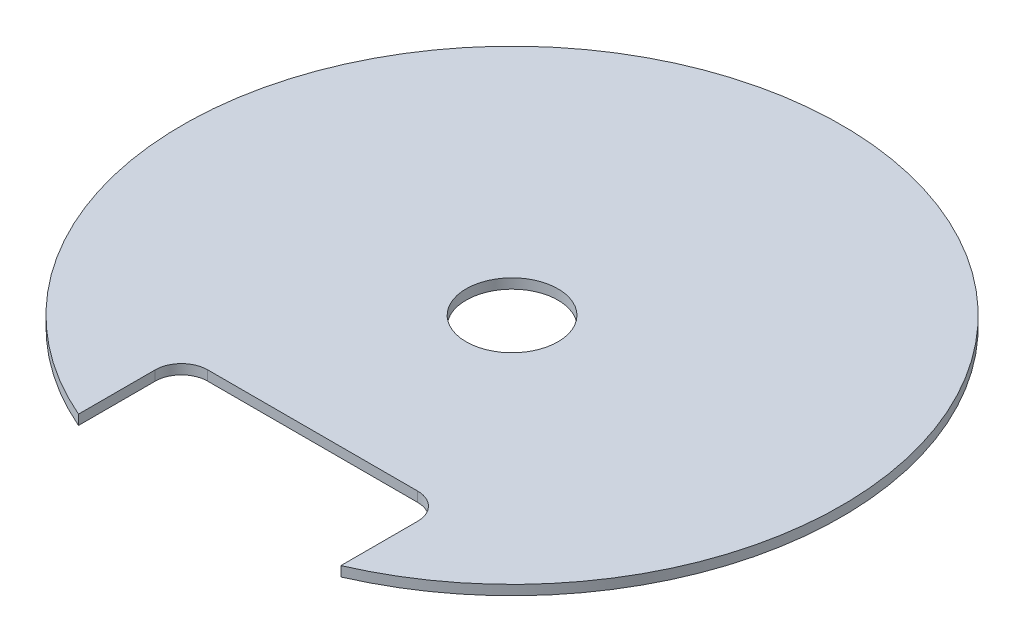
SolidWorks part; units mm, degrees
ref_plane "Front Plane" through (0, 0, 0) normal (0, 0, 1) x (1, 0, 0)
ref_plane "Top Plane" through (0, 0, 0) normal (0, 1, 0) x (1, 0, 0)
ref_plane "Right Plane" through (0, 0, 0) normal (1, 0, 0) x (0, 0, -1)
sketch "Sketch1" plane through (0, 0, 0) normal (0, 1, 0) x (1, 0, 0)
  circle A0 centre (0, 0) radius 50.25
  circle A1 centre (0, 0) radius 7
  dimension "D1" = 100.5
  dimension "D2" = 14
extrude "Boss-Extrude1" add sketch "Sketch1" against normal blind 1.5
sketch "Sketch2" plane through (0, 0, 0) normal (0, 1, 0) x (1, 0, 0)
  line L0 (-20, -46.2619) -> (-20, -34.4) construction
  line L1 (-16, -30.4) -> (16, -30.4) construction
  line L2 (20, -34.4) -> (20, -46.2619) construction
  line L3 (20, -34.4) -> (20, -46.2619)
  line L4 (-16, -30.4) -> (16, -30.4)
  line L5 (-20, -46.2619) -> (-20, -34.4)
  arc A0 (-16, -30.4) -> (-20, -34.4) centre (-16, -34.4) ccw construction
  arc A1 (20, -34.4) -> (16, -30.4) centre (16, -34.4) ccw construction
  arc A2 (20, -34.4) -> (16, -30.4) centre (16, -34.4) ccw
  arc A3 (-16, -30.4) -> (-20, -34.4) centre (-16, -34.4) ccw
  circle A4 centre (0, 0) radius 50.4 construction
  arc A5 (-20, -46.2619) -> (20, -46.2619) centre (0, 0) ccw
extrude "Cut-Extrude1" cut sketch "Sketch2" against normal through all
equation "\"pelletWidth\"= 13mm'The Width of the pellet to be dispensed"
equation "\"pelletLength\"= 26mm'The length of the pellet to be dispensed"
equation "\"pelletThickness\"= 13mm'The Thickness of the pellet to be dispensed"
equation "\"pelletRadius\"= 10mm'The roundness / radius of the pellet to be dispensed"
equation "\"rotatingPlateDiameter\"= 100mm'the diameter of the rotating plate"
equation "\"rotatingPlateHeight\"= (\"pelletThickness\"*0.9)'The thickness of the rotating plate"
equation "\"rotatingPlateDiameterAllowance\"= 0.5mm'Allowance around the edge of the rotating plate"
equation "\"rotatingPlateAgitatorDiameter\"= ( \"rotatingPlateDiameter\"-((\"pelletWidth\"*1.3)*2.5) )'The diameter of the \"agitator\" section of the rotating plate"
equation "\"rotatingPlateAgitatorHeight\"= 80mm'The height of the \"agitator\" section of the rotating plate"
equation "\"rotatingPlateAgitatorBladeThickness\"= 4mm'The thickness of the blade on the \"agitator\" section of the rotating plate"
equation "\"rotatingPlateAgitatorBladeDistance\"= ( (\"rotatingPlateAgitatorDiameter\"+ 20mm) - (\"rotatingPlateAgitatorDiameter\") )'The distance offset of the blade from the surface of the \"agitator\" section of the rotating plate"
equation "\"rotatingPlateAgitatorBladeBottomGap\"= ( \"pelletThickness\"*1.2 )'The gap between the bottom of the blade and the base of the plate on the \"agitator\" section of the rotating plate"
equation "\"rotatingPlateAgitatorBladesNumber\"= ( 3 )'The number of blades on the \"agitator\" section of the rotating plate"
equation "\"hopperBaseChamferAngle\"= 60deg'Angle of the chamfer of the Hopper base Toward the plate"
equation "\"hopperBaseLipOverhang\"= 5mm'The overhang amount of the hopper base lip"
equation "\"hopperBaseLipDepth\"= 5mm'The depth of the hopper base's overhang lip"
equation "\"hopperBaseLockNotchWidth\"= 10mm'The width of the hopper base \"lock\" notch to prevent rotation"
equation "\"hopperBaseLockNotchHeight\"= 10mm'The height of the hopper base \"lock\" notch to prevent rotation"
equation "\"hopperBaseRearNotchHeight\"= 8mm'The height of the rear snap-lock notch on the hopper base"
equation "\"hopperBaseRearNotchWidth\"= 8mm'The width of the rear snap-lock notch on the hopper base"
equation "\"hopperTankWallThickness\"= 5mm'The wall thickness of the hopper tank where pellet reserve will be stored"
equation "\"hopperTankDiameter\"= ( \"rotatingPlateDiameter\"*1.8 )'**Must be greater than \"rotatingPlateDiameter\" -- The inner diameter of the hopper tank where pellet reserve will be stored"
equation "\"hopperTankHeight\"= 200mm'The height of the hopper tank where pellet reserve will be stored"
equation "\"hopperTankCoverThickness\"= 10mm'The thickness of the Hopper Tank's cover"
equation "\"hopperTankCoverHandleLength\"= 60mm'The length of the handles on the hopper tank cover"
equation "\"hopperTankCoverHandleWidth\"= 20mm'The width of the handles on the hopper tank cover, defined as the offset from the cover's main edge"
equation "\"motorMountOffset\"= 30mm'The distance offset of the motor mount part from the hopper tank's outer edge"
equation "\"motorMountHeight\"= (\"motorHeight\" + \"motorFacePlateThickness\" + 0mm)'The height / thickness of the motor mount part"
equation "\"motorDiameter\"= 35mm'The Diameter of the main motor unit"
equation "\"motorHeight\"= 13.4mm'The height of the main motor unit"
equation "\"motorConnectorWidth\"= 10mm'The width of the motor's electrical cable connector"
equation "\"motorConnectorLength\"= 8mm'The length of the motor's electrical cable connector"
equation "\"motorConnectorHeight\"= 5mm'The height of the motor's electrical cable connector"
equation "\"motorFacePlateLength\"= 50mm'The length of the motor faceplate"
equation "\"motorFacePlateWidth\"= 10mm'The width of the motor faceplate"
equation "\"motorFacePlateThickness\"= 1mm'The thickness of the motor faceplate"
equation "\"motorFacePlateCenterRadius\"= 20mm'The rounding radius of the motor faceplate center"
equation "\"motorFacePlateEndRadius\"= 10mm'The rounding radius of the motor faceplate ends"
equation "\"motorFacePlateMountingHoleDiameter\"= 6mm'The diameter of the motor faceplate's mounting holes"
equation "\"motorFacePlateMoutingHoleDistanceBetweenHoles\"= 42mm'The distance between the center of the mounting holes"
equation "\"motorSpindleDiameter\"= 2mm'The diameter of the motor spindle"
equation "\"motorSpindleFlatFaceLength\"= 1.5mm'The length of the flat face of the motor spindle"
equation "\"motorSpindleHeight\"= 9mm'The height of the motor spindle from the face of the motor"
equation "\"motorSpindleMountDiameter\"= 12mm'The diameter of the raised mount section of the motor where the spindle is attached"
equation "\"motorSpindleMountHeight\"= 1.5mm'The height of the raised mount section of the motor where the spindle is attached"
equation "\"generalFittingTolerance\"= 0.1mm'The general fitting tolerance between contacting parts"
equation "\"D1@Sketch1\"=\"rotatingPlateDiameter\"+\"rotatingPlateDiameterAllowance\""
equation "\"D2@Sketch1\"=\"motorSpindleMountDiameter\"+2"
equation "\"D1@Boss-Extrude1\"=\"motorSpindleMountHeight\""
equation "\"rotatingPlatePelletSlotLength\"= \"pelletLength\"*1.3'The length of the slot where a pellet will be captured"
equation "\"rotatingPlatePelletSlotWidth\"= \"pelletWidth\"*1.3'The width of the slot where a pellet will be captured"
equation "\"rotatingPlateNumberOfPelletSlots\"= ( (2*pi*(\"rotatingPlateDiameter\"/2)) / ((\"rotatingPlatePelletSlotLength\"*1.1)*3) )'The maximum number of pellet slots allows in the rotating plate for proper spacing"
equation "\"rotatingPlateAgitatorTopRoundingRadius\"= 6mm'The rounding radius of the top of the \"agitator\" section of the rotating plate"
equation "\"hopperBaseInnerDiameter\"= (\"rotatingPlateDiameter\") + (\"rotatingPlateDiameterAllowance\"*2)'Diameter of the Base of the hopper where it meets the motor mount + rotating plate"
equation "\"hopperBaseOuterDiameter\"= (\"hopperBaseInnerDiameter\" + (\"hopperTankWallThickness\"*2) + 60mm)'Diameter of the Base of the hopper where it meets the motor mount + rotating plate"
equation "\"hopperBasePelletBlockerMountingSlotWidth\"= 5mm'The width of the pellet blocker mounting slot on the hopper base"
equation "\"hopperBasePelletBlockerMountingSlotOffsetFromTopOfChamfer\"= 15mm'The distance offset of the top of the pellet blocker mounting slot from the top of the hopper base chamfer"
equation "\"hopperBasePelletBlockerMountingSlotOffsetFromBottomOfChamfer\"= 10mm'The distance offset of the bottom of the pellet blocker mounting slot from the bottom of the hopper base chamfer"
equation "\"motorMountPelletThroughHoleLength\"= 40mm'The length of the pellet throughhole that routes through the motor mount and other parts"
equation "\"motorMountPelletThroughHoleWidth\"= 20mm'The width of the pellet throughhole that routes through the motor mount and other parts"
equation "\"irBeamUnitLength\"=20mm'The legth of the IR beam unit"
equation "\"irBeamUnitWidth\"=10mm'The width of the IR beam unit"
equation "\"irBeamUnitHeight\"=8mm'The height of the IR beam unit"
equation "\"irBeamUnitSlotWidth\"=2.03mm'The width of the slots on the outside of the IR beam unit"
equation "\"irBeamUnitSlotLength\"=5.10mm'The length of the slots of the outside of the IR beam unit"
equation "\"irBeamUnitSlotDepth\"=0.76mm'The depth of the slots on the outside of the IR beam unit"
equation "\"irBeamUnitSlotChamferAngle\"=45deg'The angle of the \"end\" of the slot on the outside of the IR beam unit"
equation "\"irBeamUnitSideSlotsDistanceFromBottom\"=3.98mm'The distance of the side slots on the outside of the IR beam unit from the bottom edge of the unit"
equation "\"irBeamUnitMountHoleDistanceFromBottom\"=5mm'The distance of the center mounting throughhole of the IR beam unit from the bottom edge of the unit"
equation "\"irBeamUnitMountHoleDiameter\"=2.40mm'The diameter of the center mounting throughhole of the IR beam unit"
equation "\"irBeamUnitMountHoleChamferDiameter\"=5.30mm'The diameter of the chamfer of the center mounting throughole of the IR beam unit"
equation "\"irBeamUnitMountHoleChamferDepth\"=2.65mm'The depth of the chamfer of the center mounting throughole of the IR beam unit"
equation "\"irBeamUnitLEDDistanceFromBottom\"=15mm'The distance of the center of the LED from the bottom edge of the IR beam unit"
equation "\"irBeamUnitLEDMountDiameter\"=8mm'The diameter of the LED mounting base of the IR beam unit"
equation "\"irBeamUnitLEDMountHeight\"=1.02mm'The height of the LED mounting base of the IR beam unit"
equation "\"irBeamUnitLEDDiameter\"=3.00mm'The diameter of the LED of the IR beam unit"
equation "\"irBeamUnitLEDFlatSectionHeight\"=0.65mm'The height of the \"flat\" section of the LED of the IR beam unit"
equation "\"irBeamUnitLEDDomeSectionDiameter\"=\"irBeamUnitLEDDiameter\"'The diameter of the \"domed\" section of the LED of the IR beam unit"
equation "\"irBeamUnitMountingPlateThickness\"=2mm'The thickness of the IR beam unit mounting plate"
equation "\"irBeamUnitMountingPlateAdjustmentSlotLength\"=10mm'The length of the variable/adjustable mounting slot of the IR beam unit mounting plate"
equation "\"pelletBlockerBaseWidth\"= (\"rotatingPlatePelletSlotWidth\"+\"rotatingPlateDiameterAllowance\")*1.1'The width of the base of the pellet blocker where it meets the rotating plate & pellet slot"
equation "\"pelletBlockerBaseLength\"= \"rotatingPlatePelletSlotLength\"*1.1'The length of the base of the pellet blocker where it meets the rotating plate & pellet slot"
equation "\"pelletBlockerBaseRoundingRadius\"= \"pelletWidth\"*0.5'The rounding radius of the base of the pellet blocker where it meets the rotating plate & pellet slot"
equation "\"pelletBlockerBaseHeight\"= \"rotatingPlateAgitatorBladeBottomGap\"*0.75'The height of the base of the pellet blocker where it meets the rotating plate & pellet slot"
equation "\"pelletBlockerNeckLength\"= 50mm'The length of the neck of the pellet blocker"
equation "\"pelletBlockerNeckTopRoundingRadius\"=2mm'The rounding radius of the top of the neck of the pellet blocker"
equation "\"pelletOutletTrackMountingPlateThickness\"= 2mm'The thickness of the Pellet Outlet Track Mounting Plate"
equation "\"pelletOutletTrackMountingPlateHingeHeight\"= (\"irBeamUnitWidth\" + \"irBeamUnitMountingPlateThickness\" + 2mm )'The height of the bottom of the hinge of the Pellet Outlet Mounting Plate"
equation "\"pelletOutletTrackMountingPlateHingeDiameter\"= 6mm'The inner diameter of the hinge on the Pellet Outlet Mounting Plate"
equation "\"pelletOutletTrackMountingPlateHingeOffsetFromHoleDistance\"= (\"pelletOutletTrackMountingPlateHingeDiameter\" + \"pelletOutletTrackMountingPlateThickness\" + 4mm)'The distance offset of the hinge of the Pellet Outlet Mounting Plate from the plate's mounting hole position"
equation "\"pelletOutletTrackHingeWidth\"= 10mm'The width of the pellet outlet track's hinge which mates with the hinge on the mounting plate"
equation "\"pelletOutletTrackHingeOffsetFromIRBeamUnitEdge\"= 6mm'The distance offset of the pelletOutletTrack's mating hinge from the edge of the IR Beam Unit"
equation "\"pelletOutletTrackEndingWidth\"= 50mm'The width of the pellet outlet Track at the end of the Track"
equation "\"pelletOutletTrackEndingLength\"= 30mm'The length of pellet outlet Track at the end of the Track"
equation "\"pelletOutletTrackWallHeight\"= 15mm'The height of the side walls of the pellet outlet Track"
equation "\"pelletOutletTrackThickness\"= 2mm'The thickness of the pellet outlet Track"
equation "\"baseStandMountingFaceHeight\"= 10mm'The height / thickness of the mounting face between the Base Stand and the Motor Mount parts"
equation "\"baseStandOpeningAngle\"= 55deg'The angle of the opening in the front of the Base Stand to allow for unobstructed pellet outlet"
equation "\"baseStandWallThickness\"= 10mm'The wall thickness of the Base Stand"
equation "\"baseStandHeight\"= 100mm'The overall height of the Base Stand part"
equation "\"baseStandFootDiameterOffset\"= 40mm'The distance offset of the Base Stand's foot ring"
equation "\"baseStandFootHeight\"= 20mm'The height / thickness of the Base Stand's foot ring"
